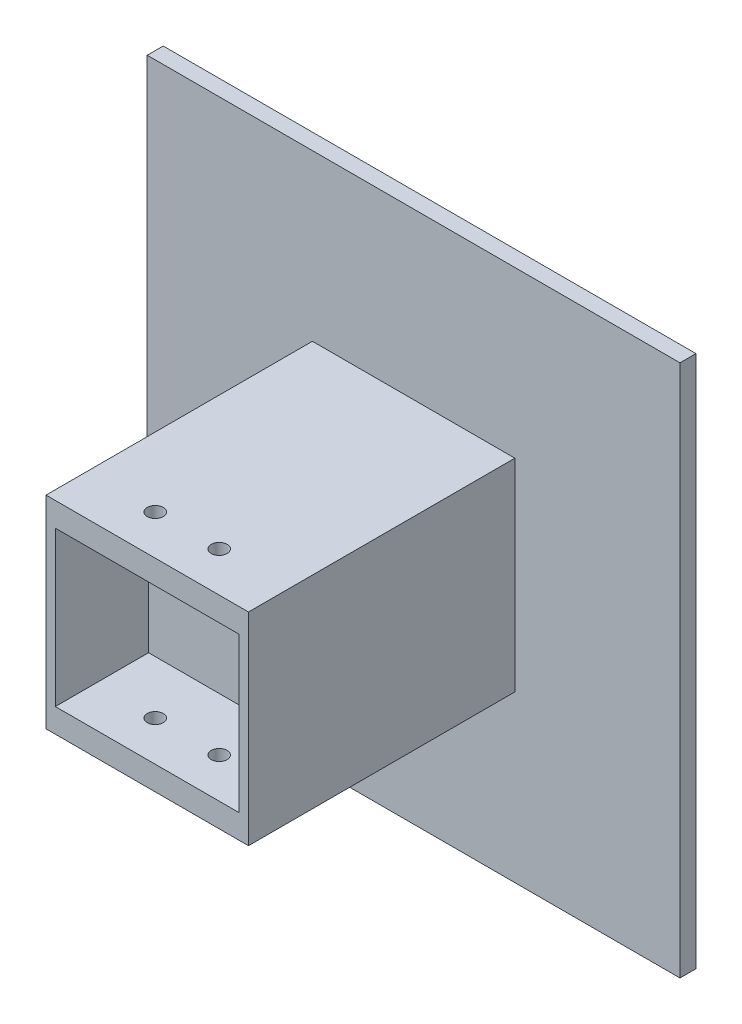
SolidWorks part; units mm, degrees
material "ABS"
ref_plane "Front Plane" through (0, 0, 0) normal (0, 0, 1) x (1, 0, 0)
ref_plane "Top Plane" through (0, 0, 0) normal (0, 1, 0) x (1, 0, 0)
ref_plane "Right Plane" through (0, 0, 0) normal (1, 0, 0) x (0, 0, -1)
sketch "Sketch1" plane through (0, 0, 0) normal (0, 0, 1) x (1, 0, 0)
  line L1 (-50, 50) -> (50, 50)
  line L2 (-50, 50) -> (-50, -50)
  line L3 (-50, -50) -> (50, -50)
  line L4 (50, 50) -> (50, -50)
  line L5 (0, -50) -> (0, 50) construction
  line L6 (-50, 0) -> (50, 0) construction
  point P0 (0, 0)
  dimension "D1" = 100
extrude "Boss-Extrude1" add sketch "Sketch1" along normal blind 3
sketch "Sketch3" plane through (0, 0, 3) normal (0, 0, 1) x (1, 0, 0)
  line L1 (-19, 19) -> (19, 19)
  line L2 (-19, 19) -> (-19, -19)
  line L3 (-19, -19) -> (19, -19)
  line L4 (19, 19) -> (19, -19)
  line L5 (0, -19) -> (0, 19) construction
  line L6 (-19, 0) -> (19, 0) construction
  point P0 (0, 0)
  dimension "D1" = 38
extrude "Boss-Extrude2" add sketch "Sketch3" along normal blind 50
sketch "Sketch5" plane through (0, 0, 53) normal (0, 0, 1) x (1, 0, 0)
  line L1 (-17.25, 14.5) -> (17.25, 14.5)
  line L2 (-17.25, 14.5) -> (-17.25, -14.5)
  line L3 (-17.25, -14.5) -> (17.25, -14.5)
  line L4 (17.25, 14.5) -> (17.25, -14.5)
  line L5 (0, -14.5) -> (0, 14.5) construction
  line L6 (-17.25, 0) -> (17.25, 0) construction
  point P0 (0, 0)
  dimension "D1" = 29
  dimension "D2" = 34.5
extrude "Cut-Extrude1" cut sketch "Sketch5" against normal blind 17.5
sketch "Sketch6" plane through (0, 19, 0) normal (0, 1, 0) x (1, 0, 0)
  line L0 (-16.6675, -45.5) -> (15.2728, -45.5)
  line L1 (19, -53) -> (-19, -53) construction
  line L2 (0, -53) -> (0, -45.5)
  line L3 (0, -45.5) -> (6, -45.5)
  circle A0 centre (6, -45.5) radius 1.5
  circle A1 centre (-6, -45.5) radius 1.5
  point P4 (0, -53)
  dimension "D1" = 7.5
extrude "Cut-Extrude2" cut sketch "Sketch6" against normal blind 50 contours A1 | A0
